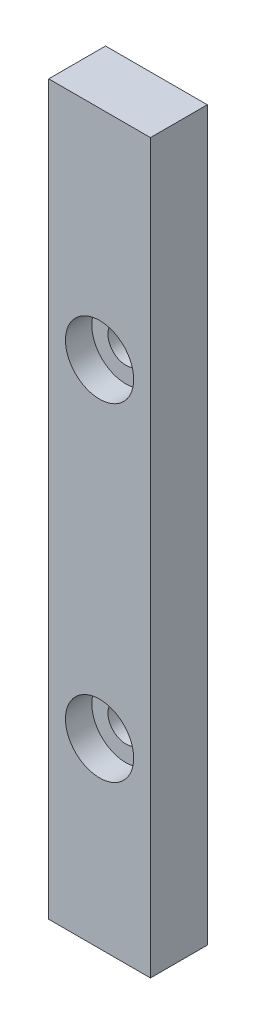
SolidWorks part; units mm, degrees
material "6061-T6 (SS)"
ref_plane "Front Plane" through (0, 0, 0) normal (0, 0, 1) x (1, 0, 0)
ref_plane "Top Plane" through (0, 0, 0) normal (0, 1, 0) x (1, 0, 0)
ref_plane "Right Plane" through (0, 0, 0) normal (1, 0, 0) x (0, 0, -1)
sketch "Sketch1" plane through (0, 0, 0) normal (0, 0, 1) x (1, 0, 0)
  line L1 (0, 0) -> (8.5, 0)
  line L2 (0, 0) -> (0, -60.8)
  line L3 (0, -60.8) -> (8.5, -60.8)
  line L4 (8.5, 0) -> (8.5, -60.8)
  dimension "D1" = 60.8
  dimension "D2" = 8.5
extrude "Boss-Extrude1" add sketch "Sketch1" along normal blind 4.75
sketch "Sketch3" plane through (0, 0, 4.75) normal (0, 0, 1) x (1, 0, 0)
  line L0 (8.5, 0) -> (0, 0) construction
  line L4 (8.5, -60.8) -> (8.5, 0) construction
  point P9 (4.25, -18.2)
  point P10 (4.25, -45.6)
  dimension "D1" = 18.2
  dimension "D2" = 27.4
  dimension "D3" = 4.25
  dimension "D4" = 4.25
hole_wizard "Ø3.0mm Dowel Hole1" positions "Sketch4" profile "Sketch5" hole size "Ø3.0" standard "ANSI Metric"
sketch "Sketch4" plane through (0, 0, 4.75) normal (0, 0, 1) x (1, 0, 0)
  point P0 (4.25, -18.2)
  point P3 (4.25, -45.6)
sketch "Sketch5" plane through (4.25, -18.2, 4.75) normal (1, 0, 0) x (0, -1, 0)
  line L0 (0, 0) -> (0, 5.9013)
  line L1 (0, 5.9013) -> (1.5, 5)
  line L2 (1.5, 5) -> (1.5, 0)
  line L5 (1.5, 0) -> (0, 0)
  line L10 (0, 5.9013) -> (-1.5, 5) construction
  line L11 (0, -6.35) -> (0, 107.95) construction
  dimension "Hole Dia." = 3
  dimension "Hole Depth" = 5
  dimension "Drill Angle" = 118
sketch "Sketch6" plane through (0, 0, 4.75) normal (0, 0, 1) x (1, 0, 0)
  circle A0 centre (4.25, -18.2) radius 2.85
  circle A1 centre (4.25, -45.6) radius 2.85
  dimension "D1" = 5.7
extrude "Cut-Extrude1" cut sketch "Sketch6" against normal blind 2.2
